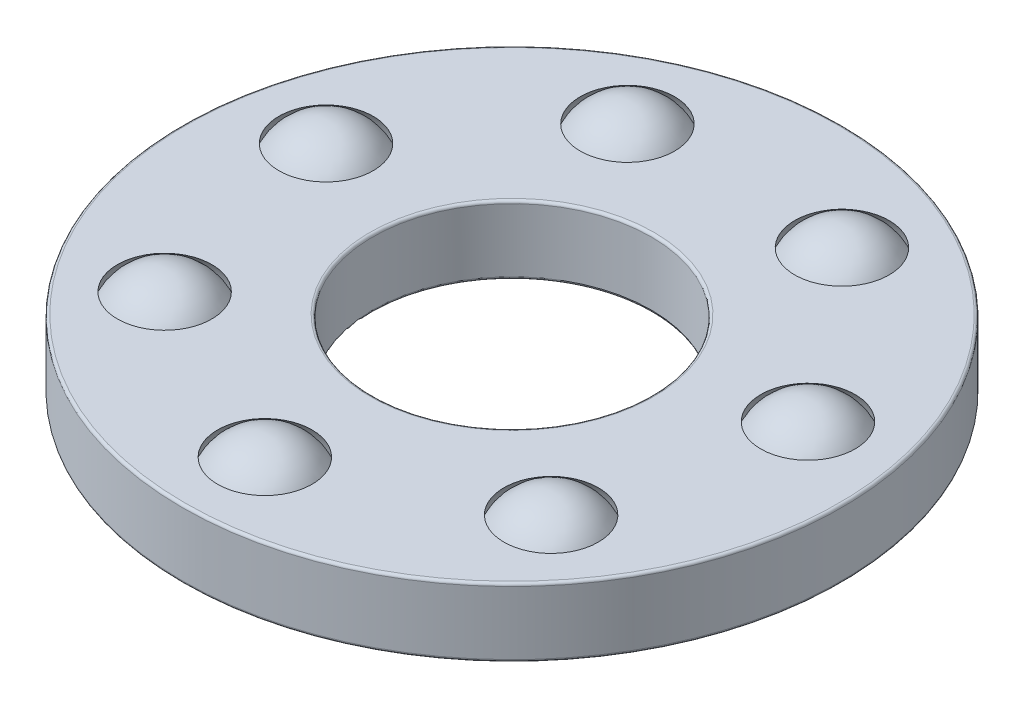
SolidWorks part; units mm, degrees
ref_plane "Front Plane" through (0, 0, 0) normal (0, 0, 1) x (1, 0, 0)
ref_plane "Top Plane" through (0, 0, 0) normal (0, 1, 0) x (1, 0, 0)
ref_plane "Right Plane" through (0, 0, 0) normal (1, 0, 0) x (0, 0, -1)
sketch "Sketch1" plane through (0, 0, 0) normal (1, 0, 0) x (0, 0, -1)
  line L0 (-6, 0) -> (6, 0) construction
  line L1 (0, -2.46) -> (0, 2.46) construction
  line L2 (-6, 0.625) -> (-2.538, 0.625)
  line L3 (-6, 0.625) -> (-6, -0.625)
  line L4 (-6, -0.625) -> (-2.538, -0.625)
  line L5 (-2.538, 0.625) -> (-2.538, -0.625)
  line L6 (-4.5, 1) -> (-4.5, -1) construction
  circle A0 centre (-4.5, 0) radius 1 construction
  dimension "D2" = 1.25
revolve "Revolve1" add sketch "Sketch1" angle 360 about L1
sketch "Sketch3" plane through (0, 0, 0) normal (1, 0, 0) x (0, 0, -1)
  line L0 (-4.5, 1.0625) -> (-4.5, -1.0625)
  line L1 (-4.5, 1) -> (-4.5, -1) construction
  line L2 (-4.4375, 1.0607) -> (-4.4375, -1.0607) construction
  arc A0 (-4.5, 1) -> (-4.5, -1) centre (-4.5, 0) ccw construction
  circle A1 centre (-4.5, 0) radius 1 construction
  arc A2 (-4.5, 1.0625) -> (-4.5, -1.0625) centre (-4.5, 0) ccw
  arc A3 (-4.4375, 1.0607) -> (-4.4375, -1.0607) centre (-4.5, 0) ccw construction
  dimension "D1" = 0.0625
revolve "Cut-Revolve1" cut sketch "Sketch3" angle 360 about L0
sketch "Sketch2" plane through (0, 0, 0) normal (1, 0, 0) x (0, 0, -1)
  line L0 (-4.5, 1) -> (-4.5, -1)
  arc A0 (-4.5, 1) -> (-4.5, -1) centre (-4.5, 0) ccw
  circle A2 centre (-4.5, 0) radius 1 construction
revolve "Revolve2" add sketch "Sketch2" angle 360 about L0
ref_axis "Axis1" through (0, 2.46, 0) along (0, -1, 0)
pattern_circular "CirPattern1" count 7 every 51.429 about axis through (0, 2.46, 0) along (0, -1, 0) of bodies 187
pattern_circular "CirPattern2" count 7 every 51.429 about axis through (0, 0, 0) along (0, 1, 0) of "Cut-Revolve1"
sketch "Sketch4" plane through (0, 0, 0) normal (1, 0, 0) x (0, 0, -1)
  line L0 (-6, 0.625) -> (-6, -0.625) construction
  line L1 (-6, 1) -> (-2.538, 1)
  line L2 (-6, 1) -> (-6, 2.46)
  line L3 (-6, 2.46) -> (-2.538, 2.46)
  line L4 (-2.538, 1) -> (-2.538, 2.46)
  line L5 (-6, -2.46) -> (-2.538, -2.46)
  line L6 (-6, -2.46) -> (-6, -1)
  line L7 (-6, -1) -> (-2.538, -1)
  line L8 (-2.538, -2.46) -> (-2.538, -1)
  line L10 (-2.538, 0.625) -> (-2.538, -0.625) construction
  line L11 (0, 0) -> (-6, 0) construction
  line L12 (-6, 0) -> (6, 0) construction
  dimension "Ht" = 4.92
  dimension "Washer Thickness" = 1.46
revolve "Revolve3" add sketch "Sketch4" angle 360 about L1
fillet "Fillet1" radius 0.0492 4 edges at (0, 1, -2.538) (0, 2.46, -2.538) (0, 1, -6) (0, 2.46, -6)
fillet "Fillet2" radius 0.0492 4 edges at (0, -0.625, -2.538) (0, 0.625, -2.538) (0, -0.625, -6) (0, 0.625, -6)
fillet "Fillet3" radius 0.0492 4 edges at (0, -2.46, -2.538) (0, -1, -2.538) (0, -2.46, -6) (0, -1, -6)
delete or keep bodies "Body-Delete/Keep 1" type delete bodies bodies 211 210
ref_plane "Plane1" through (0, -1, 0) normal (0, -1, 0) x (-1, 0, 0)
ref_plane "Plane2" through (0, 1, 0) normal (0, 1, 0) x (1, 0, 0)
equation "\"D2@Sketch1\" = \"Roller Ball Dia@Sketch1\"*.625"
equation "\"Angle@CirPattern1\" = 360/\"Balls@CirPattern1\""
equation "\"D1@CirPattern2\" = \"Balls@CirPattern1\""
equation "\"D2@CirPattern2\" = \"Angle@CirPattern1\""
equation "\"D1@Fillet1\" = \"Th@Sketch1\"*.01"
equation "\"D1@Fillet2\" = \"D1@Fillet1\""
equation "\"D1@Fillet3\" = \"D1@Fillet1\""
